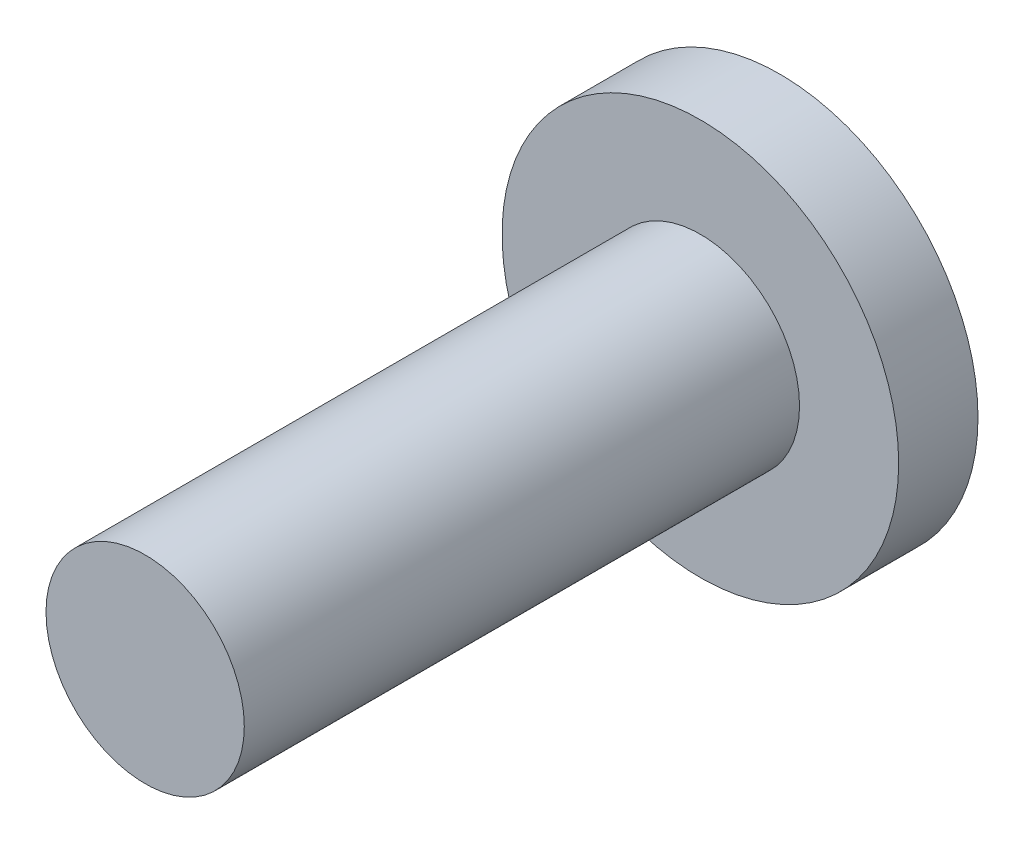
SolidWorks part; units mm, degrees
ref_plane "Front Plane" through (0, 0, 0) normal (0, 0, 1) x (1, 0, 0)
ref_plane "Top Plane" through (0, 0, 0) normal (0, 1, 0) x (1, 0, 0)
ref_plane "Right Plane" through (0, 0, 0) normal (1, 0, 0) x (0, 0, -1)
sketch "Sketch1" plane through (0, 0, 0) normal (0, 0, 1) x (1, 0, 0)
  circle A0 centre (0, 0) radius 1.25
  dimension "D1" = 2.5
extrude "Boss-Extrude1" add sketch "Sketch1" along normal blind 7
sketch "Sketch2" plane through (0, 0, 0) normal (0, 0, 1) x (1, 0, 0)
  circle A0 centre (0, 0) radius 2.5
  dimension "D1" = 5
extrude "Boss-Extrude2" add sketch "Sketch2" against normal blind 1
